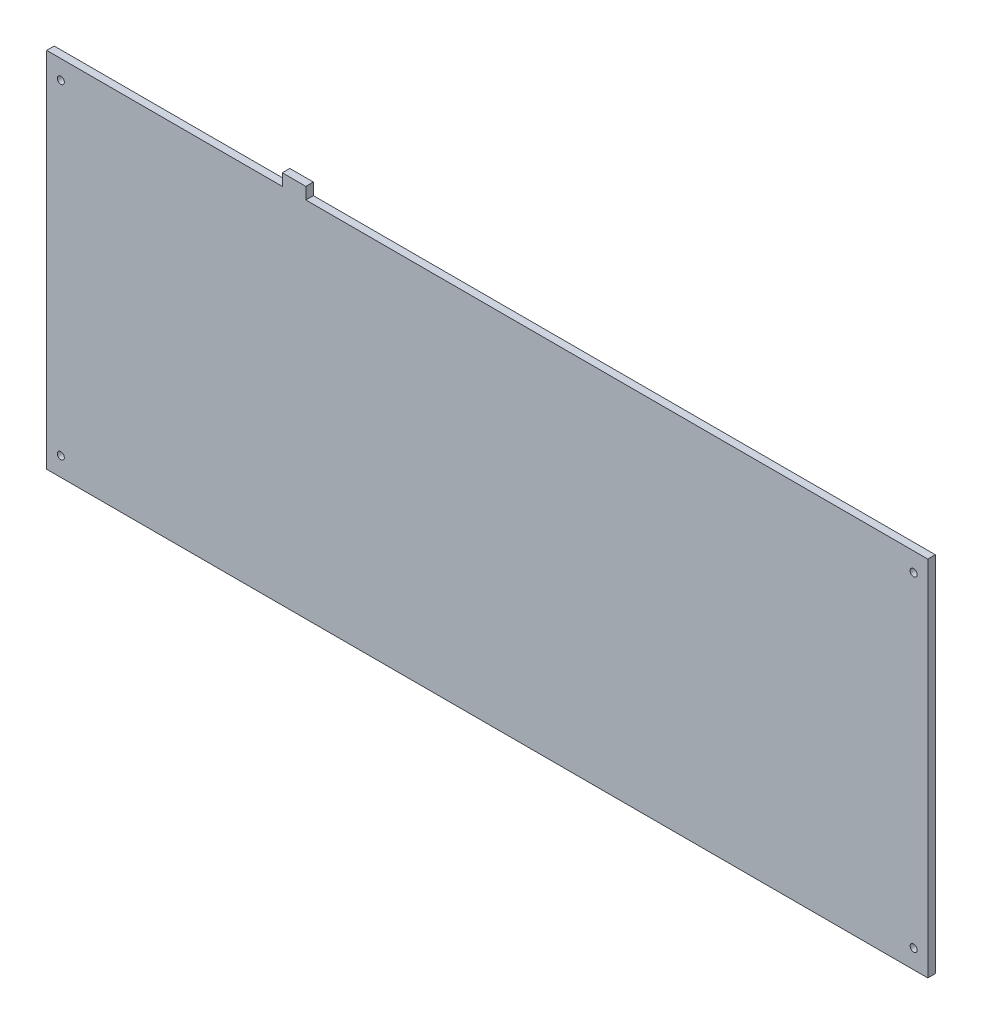
SolidWorks part; units mm, degrees
ref_plane "Спереди" through (0, 0, 0) normal (0, 0, 1) x (1, 0, 0)
ref_plane "Сверху" through (0, 0, 0) normal (0, 1, 0) x (1, 0, 0)
ref_plane "Справа" through (0, 0, 0) normal (1, 0, 0) x (0, 0, -1)
sketch "KeepOutLayer" plane through (0, 0, 0) normal (0, 0, 1) x (1, 0, 0)
  line L0 (0.0694, -77.068) -> (0.0694, -0.068)
  line L1 (0.0694, -0.068) -> (187.0694, -0.068)
  line L3 (187.0694, -77.068) -> (187.0694, -0.068)
  line L4 (0.0694, -77.068) -> (187.0694, -77.068)
  dimension "D1" = 187
  dimension "D2" = 77
  dimension "D3" = 0.068
  dimension "D4" = 0.0694
extrude "Бобышка-Вытянуть1" add sketch "KeepOutLayer" against normal blind 1.6
sketch "ViaHoleLayer" plane through (0, 0, 0) normal (0, 0, 1) x (1, 0, 0)
  line L0 (0.0694, -0.068) -> (0.0694, -77.068) construction
  line L1 (187.0694, -0.068) -> (0.0694, -0.068) construction
  line L2 (187.0694, -77.068) -> (187.0694, -0.068) construction
  line L3 (0.0694, -77.068) -> (187.0694, -77.068) construction
  circle A19 centre (3.0694, -73.068) radius 0.75
  circle A20 centre (3.0694, -4.068) radius 0.75
  circle A21 centre (184.0694, -73.068) radius 0.75
  circle A22 centre (184.0694, -4.068) radius 0.75
  dimension "D3" = 1.5
  dimension "D1" = 3
  dimension "D2" = 4
  dimension "D4" = 3
  dimension "D5" = 4
extrude "Вырез-Вытянуть1" cut sketch "ViaHoleLayer" against normal through all
sketch "Эскиз2" plane through (0, -0.068, 0) normal (0, 1, 0) x (1, 0, 0)
  line L0 (187.0694, 1.6) -> (0.0694, 1.6) construction
  line L1 (50.0694, 1.6) -> (55.0694, 1.6)
  line L2 (50.0694, 1.6) -> (50.0694, 0)
  line L3 (50.0694, 0) -> (55.0694, 0)
  line L4 (55.0694, 1.6) -> (55.0694, 0)
  line L5 (187.0694, 0) -> (0.0694, 0) construction
  line L7 (0.0694, 1.6) -> (0.0694, 0) construction
  dimension "D1" = 5
  dimension "D2" = 50
extrude "Бобышка-Вытянуть3" add sketch "Эскиз2" along normal blind 2.5
